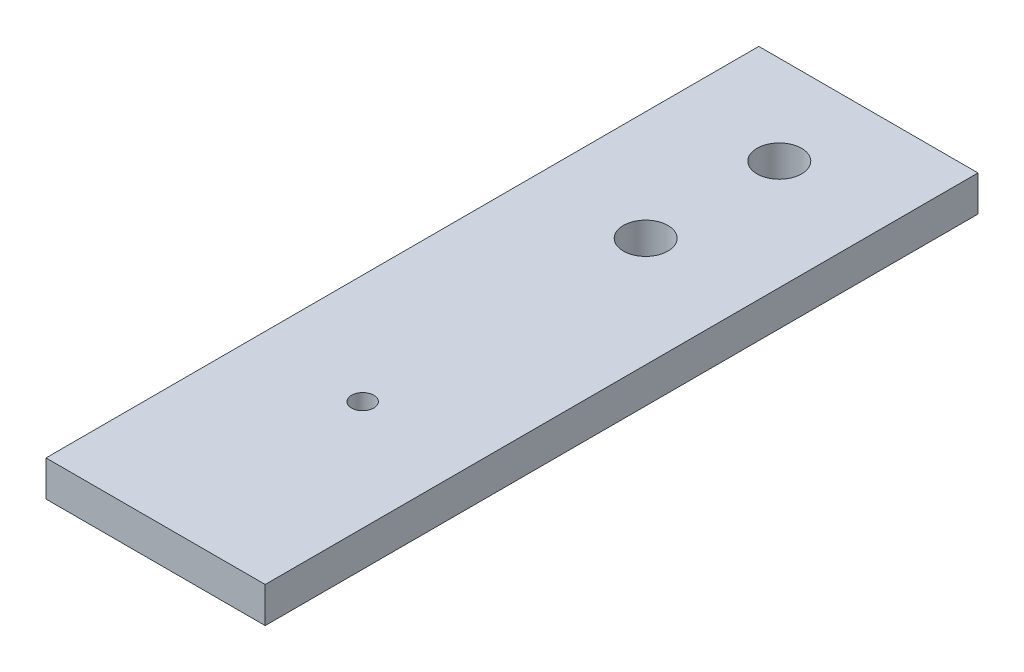
SolidWorks part; units mm, degrees
ref_plane "Front Plane" through (0, 0, 0) normal (0, 0, 1) x (1, 0, 0)
ref_plane "Top Plane" through (0, 0, 0) normal (0, 1, 0) x (1, 0, 0)
ref_plane "Right Plane" through (0, 0, 0) normal (1, 0, 0) x (0, 0, -1)
sketch "Sketch1" plane through (0, 0, 0) normal (0, 1, 0) x (1, 0, 0)
  line L1 (0, 0) -> (31.242, 0)
  line L2 (0, 0) -> (0, 101.6)
  line L3 (0, 101.6) -> (31.242, 101.6)
  line L4 (31.242, 0) -> (31.242, 101.6)
  dimension "D1" = 31.242
  dimension "D2" = 101.6
extrude "Boss-Extrude1" add sketch "Sketch1" along normal blind 5.08
sketch "Sketch2" plane through (0, 0, 0) normal (0, -1, 0) x (1, 0, 0)
  line L0 (31.242, -101.6) -> (0, -101.6) construction
  point P0 (15.621, -88.9)
  point P1 (15.621, -69.85)
  dimension "D1" = 12.7
  dimension "D2" = 19.05
hole_wizard "1/4 (0.25) Diameter Hole1" positions "Sketch3" profile "Sketch4" hole size "1/4" standard "ANSI Inch" end condition through all
sketch "Sketch3" plane through (0, 0, 0) normal (0, -1, 0) x (-1, 0, 0)
  point P0 (-15.621, 69.85)
  point P3 (-15.621, 88.9)
sketch "Sketch4" plane through (15.621, 0, -69.85) normal (1, 0, 0) x (0, 0, -1)
  line L0 (0, 0) -> (0, 5.08)
  line L1 (0, 5.08) -> (3.175, 5.08)
  line L2 (3.175, 5.08) -> (3.175, 0)
  line L5 (3.175, 0) -> (0, 0)
  line L11 (0, -6.35) -> (0, 107.95) construction
  dimension "Thru Hole Dia." = 6.35
  dimension "Thru Hole Depth" = 5.08
sketch "Sketch5" plane through (0, 0, 0) normal (0, -1, 0) x (1, 0, 0)
  line L0 (0, 0) -> (31.242, 0) construction
  line L1 (0, -101.6) -> (0, 0) construction
  line L2 (0, -57.4548) -> (31.242, -57.4548) construction
  line L3 (31.242, 0) -> (31.242, -101.6) construction
  point P2 (15.621, -29.5148)
  point P8 (15.621, -57.4548)
  dimension "D1" = 57.4548
  dimension "D2" = 31.242
  dimension "D3" = 27.94
  dimension "D4" = 15.621
hole_wizard "1/8 (0.1250) Dowel Hole1" positions "3DSketch1" profile "Sketch6" hole size "1/8" standard "ANSI Inch" end condition through all
sketch3d "3DSketch1"
  point P0 (15.621, 0, -29.5148)
sketch "Sketch6" plane through (15.621, 0, -29.5148) normal (1, 0, 0) x (0, 0, -1)
  line L0 (0, 0) -> (0, 5.08)
  line L1 (0, 5.08) -> (1.5875, 5.08)
  line L2 (1.5875, 5.08) -> (1.5875, 0)
  line L5 (1.5875, 0) -> (0, 0)
  line L11 (0, -6.35) -> (0, 107.95) construction
  dimension "Thru Hole Dia." = 3.175
  dimension "Thru Hole Depth" = 5.08
